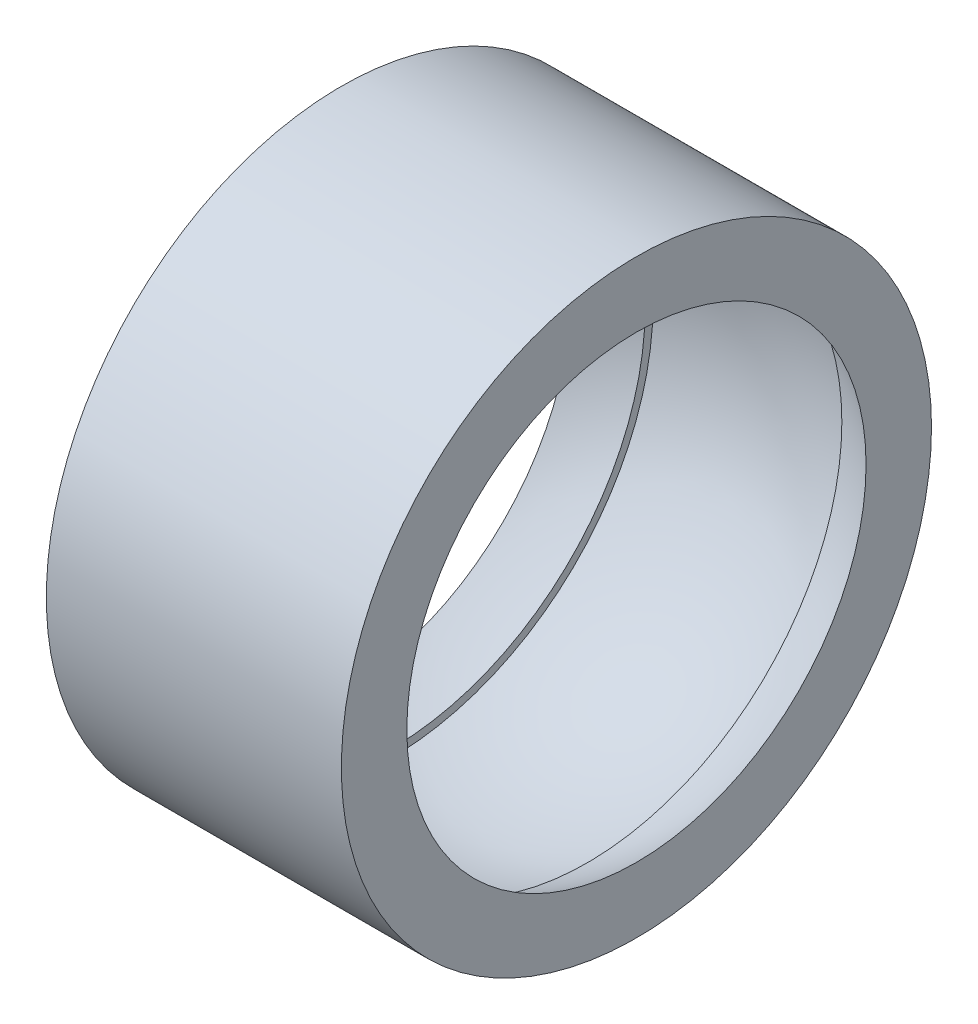
SolidWorks part; units mm, degrees
material "Brass"
ref_plane "Front Plane" through (0, 0, 0) normal (0, 0, 1) x (1, 0, 0)
ref_plane "Top Plane" through (0, 0, 0) normal (0, 1, 0) x (1, 0, 0)
ref_plane "Right Plane" through (0, 0, 0) normal (1, 0, 0) x (0, 0, -1)
sketch "Sketch1" plane through (0, 0, 0) normal (0, 0, 1) x (1, 0, 0)
  line L0 (48.3489, 0) -> (-48.3489, 0) construction
  line L1 (0, 0) -> (0, 12) construction
  line L2 (6, 12) -> (-6, 12)
  line L3 (-6, 12) -> (-6, 9.3386)
  line L4 (-4, 10.3542) -> (-4, 10.6752)
  line L6 (4, 10.3542) -> (4, 10.6752)
  line L7 (6, 12) -> (6, 9.3386)
  arc A0 (-6, 9.3386) -> (-4, 10.3542) centre (0, 0) cw
  arc A1 (6, 9.3386) -> (4, 10.3542) centre (0, 0) ccw
  arc A2 (-4, 10.6752) -> (4, 10.6752) centre (0, 0) cw
  point P14 (0, 4.3535)
  dimension "D4" = 11.1
  dimension "D5" = 11.4
  dimension "D1" = 24
  dimension "D2" = 2
  dimension "D3" = 12
revolve "Revolve1" add sketch "Sketch1" angle 360 about L0
